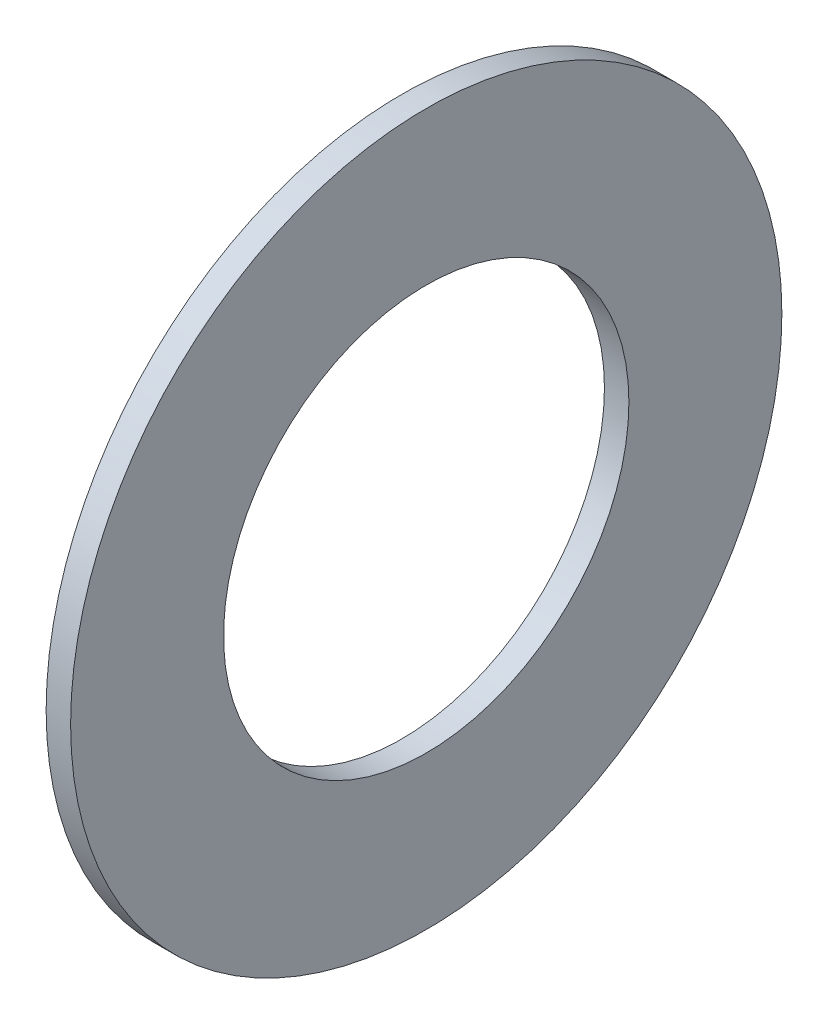
SolidWorks part; units mm, degrees
ref_plane "Front Plane" through (0, 0, 0) normal (0, 0, 1) x (1, 0, 0)
ref_plane "Top Plane" through (0, 0, 0) normal (0, 1, 0) x (1, 0, 0)
ref_plane "Right Plane" through (0, 0, 0) normal (1, 0, 0) x (0, 0, -1)
sketch "Sketch1" plane through (0, 0, 0) normal (1, 0, 0) x (0, 0, -1)
  circle A0 centre (0, 0) radius 11.811
  circle A1 centre (0, 0) radius 6.731
  dimension "OD" = 23.622
  dimension "Shaft Dia" = 13.462
extrude "Extrude1" add sketch "Sketch1" along normal blind 0.8128
